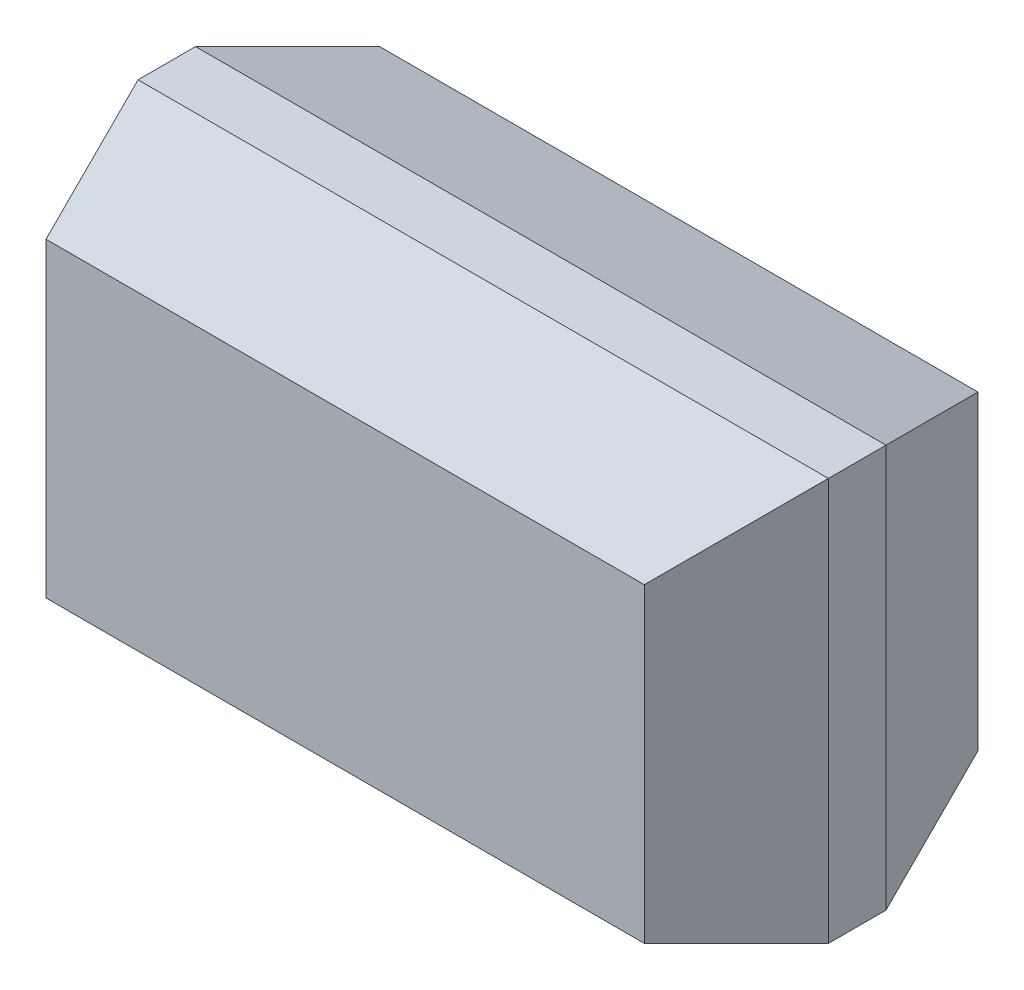
SolidWorks part; units mm, degrees
ref_plane "Plan de face" through (0, 0, 0) normal (0, 0, 1) x (1, 0, 0)
ref_plane "Plan de dessus" through (0, 0, 0) normal (0, 1, 0) x (1, 0, 0)
ref_plane "Plan de droite" through (0, 0, 0) normal (1, 0, 0) x (0, 0, -1)
sketch "Esquisse1" plane through (0, 0, 0) normal (0, 0, 1) x (1, 0, 0)
  line L1 (0, 0) -> (3, 0)
  line L2 (0, 0) -> (0, 1.75)
  line L3 (0, 1.75) -> (3, 1.75)
  line L4 (3, 0) -> (3, 1.75)
extrude "Boss.-Extru.1" add sketch "Esquisse1" along normal blind 1.45
chamfer "Chanfrein1" distance 0.6 distance2 0.2 1 edges at (1.5, 0, 1.45)
chamfer "Chanfrein2" distance 0.2 distance2 0.6 1 edges at (1.5, 0, 0)
chamfer "Chanfrein3" distance 0.6 distance2 0.2 1 edges at (1.5, 1.75, 1.45)
chamfer "Chanfrein4" distance 0.2 distance2 0.6 1 edges at (1.5, 1.75, 0)
chamfer "Chanfrein5" distance 0.6 distance2 0.2 1 edges at (0, 0.875, 1.45)
chamfer "Chanfrein6" distance 0.2 distance2 0.6 1 edges at (0, 0.875, 0)
chamfer "Chanfrein7" distance 0.6 distance2 0.2 1 edges at (3, 0.875, 1.45)
chamfer "Chanfrein8" distance 0.2 distance2 0.6 1 edges at (3, 0.875, 0)
